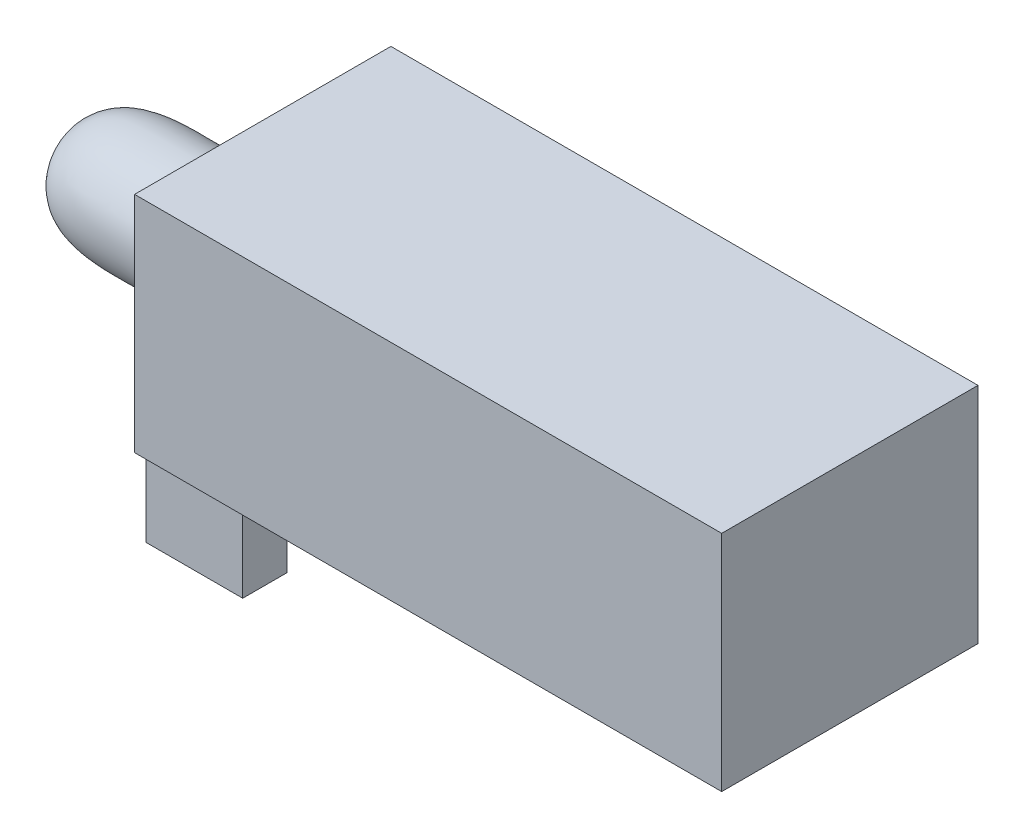
SolidWorks part; units mm, degrees
ref_plane "Front Plane" through (0, 0, 0) normal (0, 0, 1) x (1, 0, 0)
ref_plane "Top Plane" through (0, 0, 0) normal (0, 1, 0) x (1, 0, 0)
ref_plane "Right Plane" through (0, 0, 0) normal (1, 0, 0) x (0, 0, -1)
sketch "Sketch1" plane through (0, 0, 0) normal (0, 1, 0) x (1, 0, 0)
  line L1 (6.4, -2.794) -> (-6.4, -2.794)
  line L2 (6.4, -2.794) -> (6.4, 2.794)
  line L3 (6.4, 2.794) -> (-6.4, 2.794)
  line L4 (-6.4, -2.794) -> (-6.4, 2.794)
  line L5 (6.4, -2.794) -> (-6.4, 2.794) construction
  line L6 (6.4, 2.794) -> (-6.4, -2.794) construction
  point P0 (0, 0)
  dimension "D1" = 12.8
  dimension "D2" = 5.588
extrude "Boss-Extrude1" add sketch "Sketch1" along normal blind 4.8768
sketch "Sketch2" plane through (0, 0, 0) normal (0, -1, 0) x (1, 0, 0)
  line L0 (-6.4, 2.544) -> (-4.2918, 2.544)
  line L1 (-6.4, -2.794) -> (-6.4, 2.794) construction
  line L2 (-4.2918, 2.544) -> (-4.2918, 1.584)
  line L3 (-4.2918, 1.584) -> (-6.4, 1.584)
  line L4 (-6.5499, 0) -> (7.7072, 0) construction
  line L5 (-6.4, 2.794) -> (6.4, 2.794) construction
  line L6 (-4.2918, -1.584) -> (-6.4, -1.584)
  line L7 (-6.4, -2.544) -> (-4.2918, -2.544)
  line L8 (-4.2918, -2.544) -> (-4.2918, -1.584)
  line L9 (-6.4, -1.584) -> (-6.4, -2.544)
  line L10 (-6.4, 2.544) -> (-6.4, 1.584)
  dimension "D1" = 2.1082
  dimension "D2" = 0.96
  dimension "D3" = 0.25
extrude "Boss-Extrude2" add sketch "Sketch2" along normal blind 1.82
sketch "Sketch3" plane through (0, 0, 0) normal (0, -1, 0) x (1, 0, 0)
  line L0 (-6.4, 2.544) -> (-6.4, 2.794) construction
  line L1 (-6.4, 2.544) -> (-4.2918, 2.544)
  line L2 (-6.4, 2.544) -> (-6.4, -2.544)
  line L3 (-6.4, -2.544) -> (-4.2918, -2.544)
  line L4 (-4.2918, 2.544) -> (-4.2918, -2.544)
extrude "Boss-Extrude3" add sketch "Sketch3" along normal blind 0.2
ref_plane "Plane1" through (-6.5, 0, 0) normal (-1, 0, 0) x (0, 0, 1)
sketch "Sketch4" plane through (-6.5, 0, 0) normal (-1, 0, 0) x (0, 0, 1)
  line L0 (1.4142, 3.5488) -> (1.4142, 0.7204)
  arc A0 (1.4142, 3.5488) -> (1.4142, 0.7204) centre (0, 2.1346) ccw
extrude "Boss-Extrude4" add sketch "Sketch4" along normal blind 0.118 separate body
sketch "Sketch5" plane through (0, 0, 0) normal (0, 0, 1) x (1, 0, 0)
  line L0 (-6.618, 2.1346) -> (-10.618, 2.1346) construction
  line L1 (-6.618, 0.7204) -> (-6.618, 3.5488) construction
  line L2 (-6.618, 3.5488) -> (-6.618, 2.1346)
  line L3 (-6.618, 2.1346) -> (-10.618, 2.1346)
  spline S0 degree 3 poles (-10.618, 2.1346) (-10.4783, 3.6396) (-8.502, 3.2887) (-7.0335, 3.4699) (-6.618, 3.5488) knots 0 0 0 0 0.727689 1 1 1 1
  dimension "D1" = 4
revolve "Revolve1" add sketch "Sketch5" angle 360 about L0
